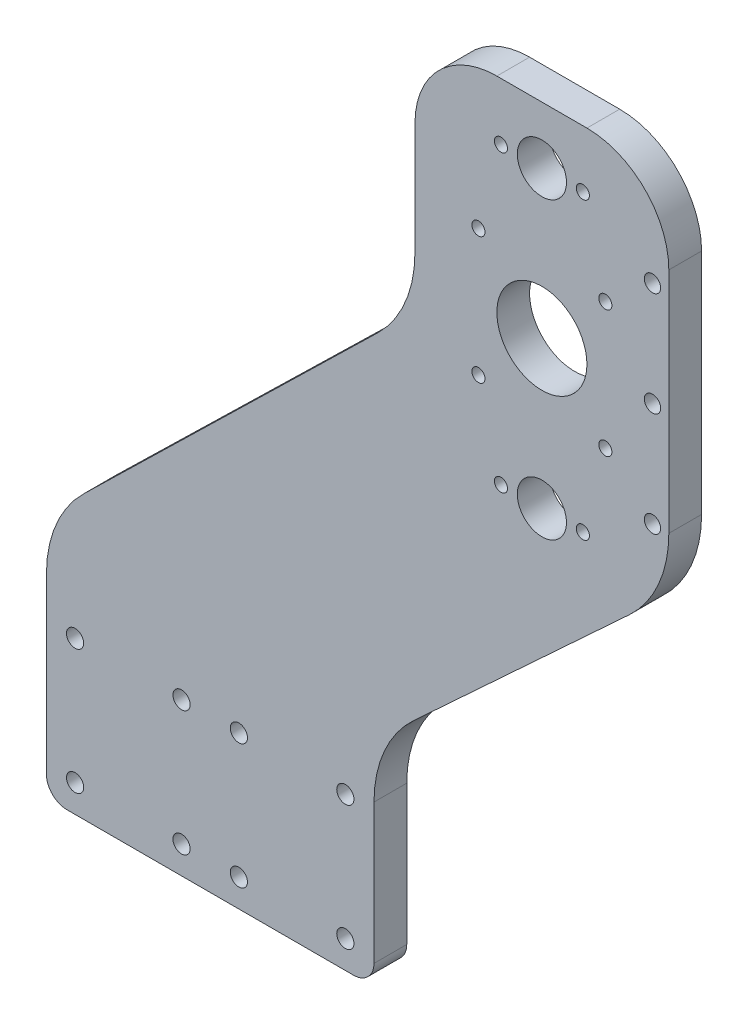
SolidWorks part; units mm, degrees
ref_plane "Front Plane" through (0, 0, 0) normal (0, 0, 1) x (1, 0, 0)
ref_plane "Top Plane" through (0, 0, 0) normal (0, 1, 0) x (1, 0, 0)
ref_plane "Right Plane" through (0, 0, 0) normal (1, 0, 0) x (0, 0, -1)
sketch "Sketch1" plane through (0, 0, 0) normal (0, 0, 1) x (1, 0, 0)
  line L0 (-23.6587, -94.3258) -> (-23.6587, -15.4242) construction
  line L1 (-58.6587, -94.3258) -> (11.3413, -94.3258)
  line L2 (-63.6587, -89.3258) -> (-63.6587, -46.9838)
  line L3 (-63.6587, -89.3258) -> (-23.6587, -89.3258) construction
  line L4 (16.3413, -89.3258) -> (16.3413, -55.2061)
  line L5 (46.3413, 113.3386) -> (68.3413, 113.3386)
  line L6 (26.3413, 93.3386) -> (26.3413, 65.9966)
  line L7 (57.3413, 113.3386) -> (57.3413, 27.3986) construction
  line L8 (88.3413, 93.3386) -> (88.3413, 37.6266)
  line L9 (-43.6587, -72.3258) -> (-43.6587, -89.3258) construction
  line L10 (-56.6587, -57.0758) -> (-30.6587, -57.0758) construction
  line L11 (17.2739, 44.5064) -> (-54.5912, -25.4936)
  line L12 (78.7126, 15.6036) -> (25.9701, -33.1831)
  line L13 (-56.6587, -57.0758) -> (-56.6587, -87.5758) construction
  line L14 (-56.6587, -87.5758) -> (-30.6587, -87.5758) construction
  line L15 (-30.6587, -57.0758) -> (-30.6587, -87.5758) construction
  line L16 (-56.6587, -57.0758) -> (-30.6587, -87.5758) construction
  line L17 (-56.6587, -87.5758) -> (-30.6587, -57.0758) construction
  line L18 (57.3413, 99.3386) -> (57.3413, 27.3986) construction
  line L20 (41.8413, 47.8686) -> (72.8413, 47.8686) construction
  line L21 (41.8413, 47.8686) -> (41.8413, 78.8686) construction
  line L22 (41.8413, 78.8686) -> (72.8413, 78.8686) construction
  line L23 (72.8413, 47.8686) -> (72.8413, 78.8686) construction
  line L24 (41.8413, 47.8686) -> (72.8413, 78.8686) construction
  line L25 (41.8413, 78.8686) -> (72.8413, 47.8686) construction
  arc A0 (78.7126, 15.6036) -> (88.3413, 37.6266) centre (58.3413, 37.6266) ccw
  arc A1 (17.2739, 44.5064) -> (26.3413, 65.9966) centre (-3.6587, 65.9966) ccw
  arc A2 (16.3413, -55.2061) -> (25.9701, -33.1831) centre (46.3413, -55.2061) cw
  arc A3 (-63.6587, -46.9838) -> (-54.5912, -25.4936) centre (-33.6587, -46.9838) cw
  arc A4 (88.3413, 93.3386) -> (68.3413, 113.3386) centre (68.3413, 93.3386) ccw
  arc A5 (46.3413, 113.3386) -> (26.3413, 93.3386) centre (46.3413, 93.3386) ccw
  arc A6 (16.3413, -89.3258) -> (11.3413, -94.3258) centre (11.3413, -89.3258) cw
  arc A7 (-58.6587, -94.3258) -> (-63.6587, -89.3258) centre (-58.6587, -89.3258) cw
  circle A8 centre (-56.6587, -57.0758) radius 2.1
  circle A9 centre (-30.6587, -57.0758) radius 2.1
  circle A10 centre (-30.6587, -87.5758) radius 2.1
  circle A11 centre (-56.6587, -87.5758) radius 2.1
  circle A12 centre (9.3413, -87.5758) radius 2.1
  circle A13 centre (-16.6587, -87.5758) radius 2.1
  circle A14 centre (-16.6587, -57.0758) radius 2.1
  circle A15 centre (9.3413, -57.0758) radius 2.1
  circle A16 centre (57.3413, 99.3386) radius 6
  circle A17 centre (57.3413, 27.3986) radius 6
  circle A18 centre (57.3413, 63.3686) radius 11
  circle A19 centre (41.8413, 78.8686) radius 1.6
  circle A20 centre (72.8413, 78.8686) radius 1.6
  circle A21 centre (72.8413, 47.8686) radius 1.6
  circle A22 centre (41.8413, 47.8686) radius 1.6
  circle A23 centre (84.3413, 37.6266) radius 2
  circle A24 centre (84.3518, 88.5185) radius 2
  circle A25 centre (47.3413, 99.3386) radius 1.6
  circle A26 centre (47.3413, 27.3986) radius 1.6
  circle A27 centre (67.3413, 99.3386) radius 1.6
  circle A28 centre (67.3413, 27.3986) radius 1.6
  circle A29 centre (84.3466, 63.0726) radius 2
  point P0 (0, 0)
  point P1 (57.3413, 82.2289)
  point P15 (26.3413, 53.3386)
  point P20 (-63.6587, -34.3258)
  point P23 (88.3413, 113.3386)
  point P26 (26.3413, 113.3386)
  point P29 (16.3413, -94.3258)
  point P32 (-63.6587, -94.3258)
  point P35 (-43.6587, -72.3258)
  dimension "D5" = 30
  dimension "D6" = 20
  dimension "D7" = 5
  dimension "D14" = 71.94
  dimension "D12" = 31
  dimension "D17" = 4
  dimension "D18" = 10
  dimension "D19" = 10
  dimension "D1" = 80
  dimension "D2" = 22
  dimension "D3" = 90
  dimension "D4" = 60
  dimension "D8" = 26
  dimension "D9" = 60
  dimension "D10" = 22
  dimension "D11" = 70
  dimension "D13" = 30.5
  dimension "D15" = 14
  dimension "D16" = 31
extrude "Boss-Extrude1" add sketch "Sketch1" along normal blind 8 contours L11 A3 L2 A7 L1 A6 L4 A2 L12 A0 L8 A4 L5 A5 L6 A1
